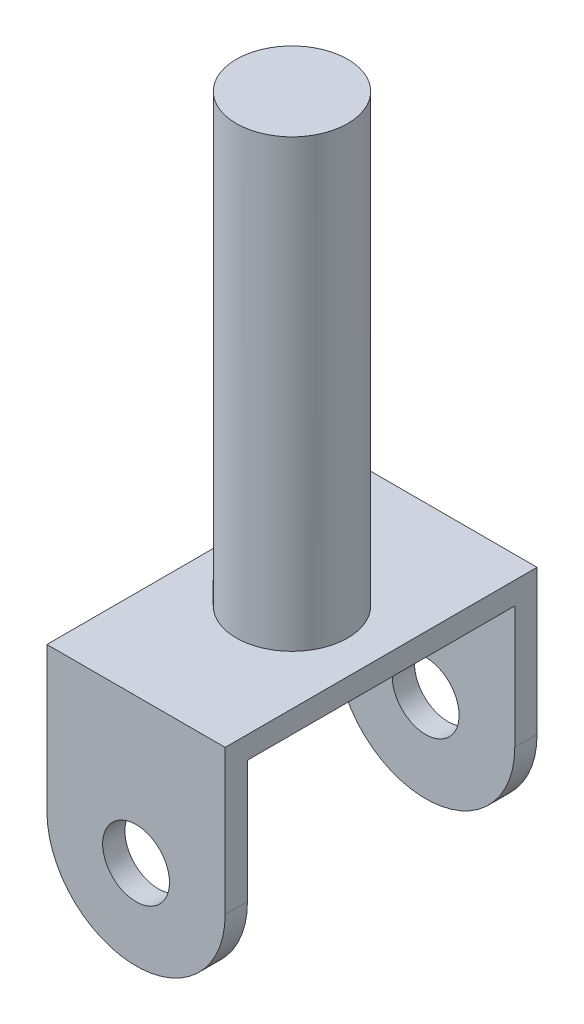
SolidWorks part; units mm, degrees
ref_plane "Plan de face" through (0, 0, 0) normal (0, 0, 1) x (1, 0, 0)
ref_plane "Plan de dessus" through (0, 0, 0) normal (0, 1, 0) x (1, 0, 0)
ref_plane "Plan de droite" through (0, 0, 0) normal (1, 0, 0) x (0, 0, -1)
sketch "Esquisse1" plane through (0, 0, 0) normal (0, 0, 1) x (1, 0, 0)
  line L0 (0, 3.5) -> (0, 10)
  line L1 (0, 10) -> (8, 10)
  line L2 (8, 10) -> (8, 3.5)
  circle A0 centre (4, 3.5) radius 1.5
  arc A1 (0, 3.5) -> (8, 3.5) centre (4, 3.5) ccw
extrude "Extrusion1" add sketch "Esquisse1" along normal blind 14
sketch "Esquisse2" plane through (0, 10, 0) normal (0, 1, 0) x (1, 0, 0)
  circle A0 centre (4, -7) radius 2.5
extrude "Extrusion2" add sketch "Esquisse2" along normal blind 20
sketch "Esquisse5" plane through (0, 0, 0) normal (-1, 0, 0) x (0, 0, 1)
  line L4 (1, 9) -> (13, 9)
  line L7 (13, 9) -> (13, -0.7836)
  line L8 (1, 9) -> (1, -0.7836)
  line L9 (1, -0.7836) -> (13, -0.7836)
extrude "Extrusion4" cut sketch "Esquisse5" against normal blind 20
